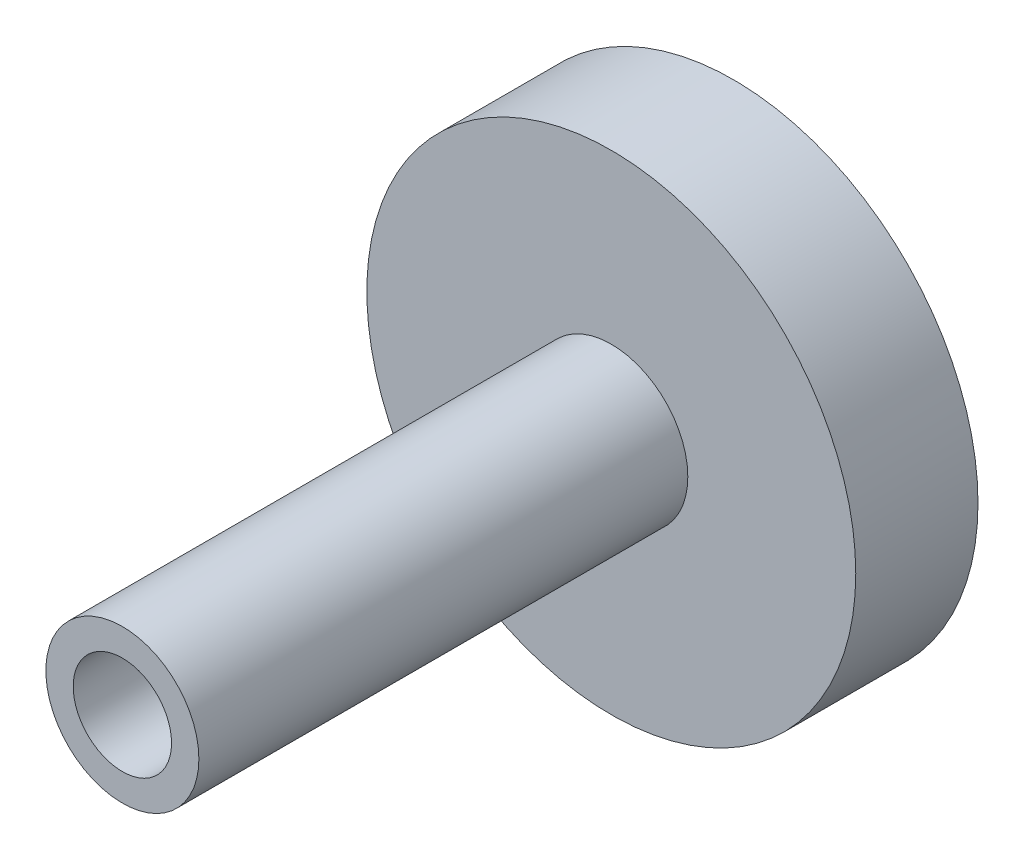
SolidWorks part; units mm, degrees
material "AISI 1020"
ref_plane "Front Plane" through (0, 0, 0) normal (0, 0, 1) x (1, 0, 0)
ref_plane "Top Plane" through (0, 0, 0) normal (0, 1, 0) x (1, 0, 0)
ref_plane "Right Plane" through (0, 0, 0) normal (1, 0, 0) x (0, 0, -1)
sketch "Sketch1" plane through (0, 0, 0) normal (0, 0, 1) x (1, 0, 0)
  circle A0 centre (0, 0) radius 12.7
  circle A1 centre (0, 0) radius 2.555
  dimension "D1" = 25.4
  dimension "D2" = 5.11
extrude "Boss-Extrude1" add sketch "Sketch1" along normal blind 31.75
cosmetic thread "Cosmetic Thread1" parameters "D2"=6.35
sketch "Sketch2" plane through (0, 0, 31.75) normal (0, 0, 1) x (1, 0, 0)
  circle A0 centre (0, 0) radius 3.9751
  circle A1 centre (0, 0) radius 12.7
  dimension "D1" = 7.9502
extrude "Cut-Extrude1" cut sketch "Sketch2" against normal blind 25.4
